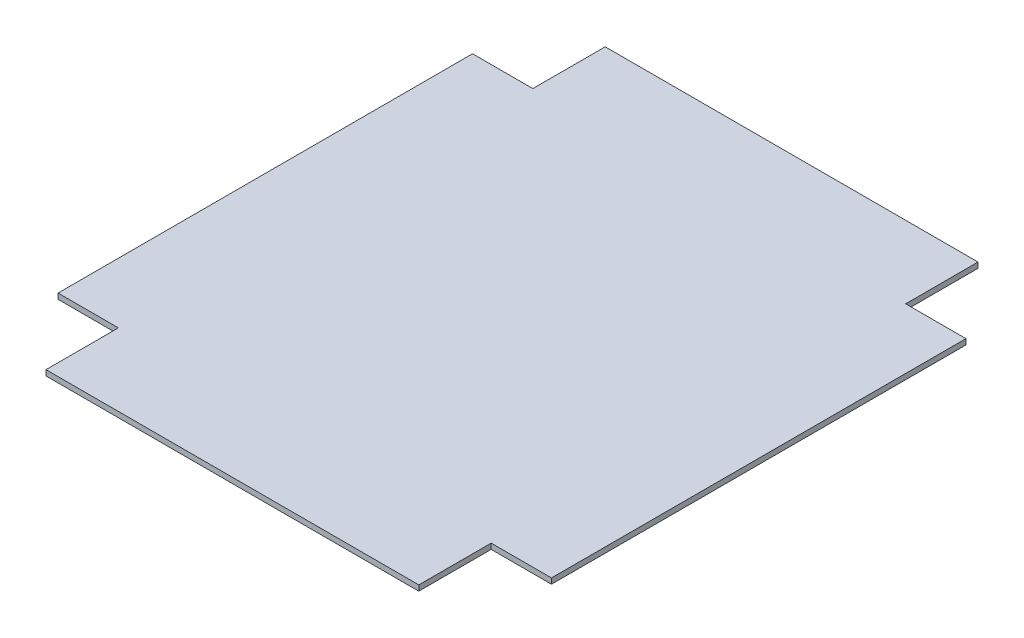
SolidWorks part; units mm, degrees
ref_plane "Front" through (0, 0, 0) normal (0, 0, 1) x (1, 0, 0)
ref_plane "Top" through (0, 0, 0) normal (0, 1, 0) x (1, 0, 0)
ref_plane "Right" through (0, 0, 0) normal (1, 0, 0) x (0, 0, -1)
sketch "Sketch1" plane through (0, 0, 0) normal (0, 1, 0) x (1, 0, 0)
  line L0 (0, 102.8458) -> (0, -136.6159) construction
  line L1 (-170, 255) -> (170, 255)
  line L2 (-225, 189) -> (-225, -189)
  line L3 (-170, -255) -> (170, -255)
  line L4 (225, 189) -> (225, -189)
  line L5 (-86.5132, 80.97) -> (246.8201, 80.97) construction
  line L9 (-225, 189) -> (-170, 189)
  line L10 (-170, 255) -> (-170, 189)
  line L11 (-92.4678, 0) -> (103.0501, 0) construction
  line L12 (-225, -189) -> (-170, -189)
  line L13 (-170, -255) -> (-170, -189)
  line L17 (170, -255) -> (170, -189)
  line L18 (225, -189) -> (170, -189)
  line L20 (225, 189) -> (170, 189)
  line L21 (170, 255) -> (170, 189)
  point P0 (0, 0)
  dimension "D3" = 55
  dimension "D4" = 66
extrude "Boss-Extrude1" add sketch "Sketch1" along normal blind 5
sketch "Sketch3" plane through (0, 5, 0) normal (0, 1, 0) x (1, 0, 0)
  line L0 (-82.4699, 84.9146) -> (250.8635, 84.9146) construction
  line L1 (16.6667, 47.5) -> (83.3333, 47.5) construction
  line L2 (-163.6919, 4.0083) -> (169.6414, 4.0083) construction
  line L3 (-34.6669, 125.9706) -> (298.6665, 125.9706) construction
  line L4 (30.6474, -126.43) -> (-302.6859, -126.43) construction
